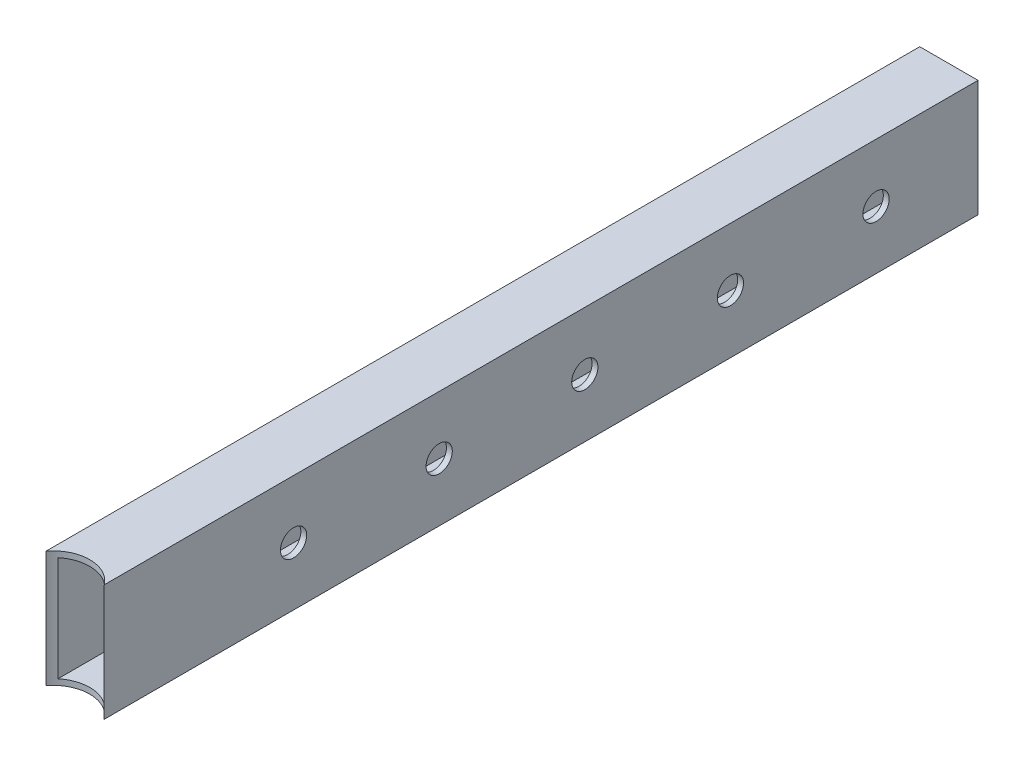
SolidWorks part; units mm, degrees
ref_plane "Спереди" through (0, 0, 0) normal (0, 0, 1) x (1, 0, 0)
ref_plane "Сверху" through (0, 0, 0) normal (0, 1, 0) x (1, 0, 0)
ref_plane "Справа" through (0, 0, 0) normal (1, 0, 0) x (0, 0, -1)
sketch "Эскиз1" plane through (0, 0, 0) normal (0, 0, 1) x (1, 0, 0)
  line L1 (-10, 20) -> (10, 20)
  line L2 (-10, 20) -> (-10, -20)
  line L3 (-10, -20) -> (10, -20)
  line L4 (10, 20) -> (10, -20)
  line L5 (-10, 20) -> (10, -20) construction
  line L6 (-10, -20) -> (10, 20) construction
  line L7 (-8, 18) -> (8, 18)
  line L8 (-8, 18) -> (-8, -18)
  line L9 (-8, -18) -> (8, -18)
  line L10 (8, 18) -> (8, -18)
  line L11 (-8, 18) -> (8, -18) construction
  line L12 (-8, -18) -> (8, 18) construction
  point P0 (0, 0)
  point P5 (0, 0)
  dimension "D1" = 20
  dimension "D2" = 40
  dimension "D3" = 2
  dimension "D4" = 2
extrude "Бобышка-Вытянуть1" add sketch "Эскиз1" along normal blind 300
sketch "Эскиз2" plane through (0, 20, 0) normal (0, 1, 0) x (1, 0, 0)
  circle A0 centre (0, -307.5) radius 12.5
  dimension "D1" = 25
extrude "Вырез-Вытянуть1" cut sketch "Эскиз2" against normal blind 40
sketch "Эскиз3" plane through (10, 0, 0) normal (1, 0, 0) x (0, 0, -1)
  line L0 (0, -20) -> (0, 20) construction
  line L1 (-300, -20) -> (0, -20) construction
  circle A0 centre (-35, 0) radius 4.5
  circle A1 centre (-85, 0) radius 4.5
  circle A2 centre (-135, 0) radius 4.5
  circle A3 centre (-185, 0) radius 4.5
  circle A4 centre (-235, 0) radius 4.5
  dimension "D1" = 50
  dimension "D6" = 9
  dimension "D2" = 50
  dimension "D3" = 50
  dimension "D4" = 50
  dimension "D5" = 35
  dimension "D7" = 20
extrude "Вырез-Вытянуть2" cut sketch "Эскиз3" against normal blind 2
